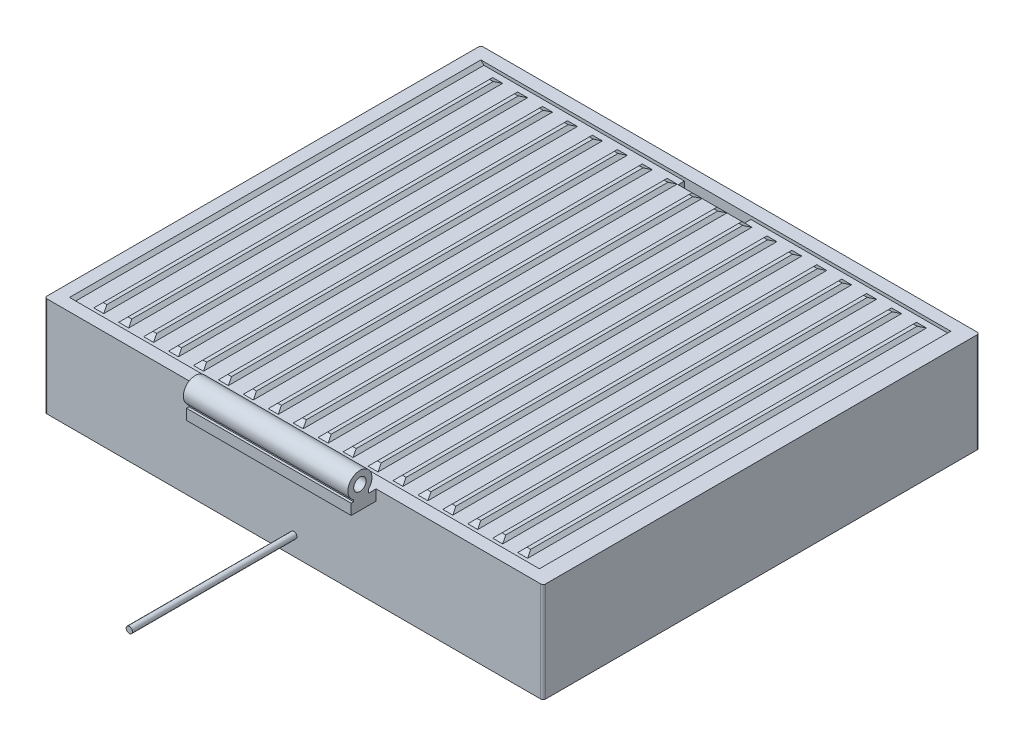
SolidWorks part; units mm, degrees
ref_plane "Front Plane" through (0, 0, 0) normal (0, 0, 1) x (1, 0, 0)
ref_plane "Top Plane" through (0, 0, 0) normal (0, 1, 0) x (1, 0, 0)
ref_plane "Right Plane" through (0, 0, 0) normal (1, 0, 0) x (0, 0, -1)
sketch "Sketch1" plane through (0, 0, 0) normal (0, 0, 1) x (1, 0, 0)
  line L1 (-200, 40) -> (200, 40)
  line L2 (-200, 40) -> (-200, -40)
  line L3 (-200, -40) -> (200, -40)
  line L4 (200, 40) -> (200, -40)
  line L5 (-200, 40) -> (200, -40) construction
  line L6 (-200, -40) -> (200, 40) construction
  point P0 (0, 0)
  dimension "D1" = 400
  dimension "D2" = 80
extrude "Boss-Extrude1" add sketch "Sketch1" along normal mid plane 350
sketch "Sketch2" plane through (0, 0, 0) normal (0, 0, 1) x (1, 0, 0)
  line L0 (200, 40) -> (-200, 40) construction
  line L1 (-190, 40) -> (-173, 40)
  line L14 (-190, 40) -> (-187.5, 37.5)
  line L15 (-187.5, 37.5) -> (-175.5, 37.5)
  line L16 (-175.5, 37.5) -> (-173, 40)
  line L17 (-173, 40) -> (-190, 40)
  line L18 (-170, 40) -> (-167.5, 37.5)
  line L19 (-167.5, 37.5) -> (-155.5, 37.5)
  line L20 (-155.5, 37.5) -> (-153, 40)
  line L21 (-170, 40) -> (-153, 40)
  line L22 (-150, 40) -> (-147.5, 37.5)
  line L23 (-147.5, 37.5) -> (-135.5, 37.5)
  line L24 (-135.5, 37.5) -> (-133, 40)
  line L25 (-150, 40) -> (-133, 40)
  line L26 (-130, 40) -> (-127.5, 37.5)
  line L27 (-127.5, 37.5) -> (-115.5, 37.5)
  line L28 (-115.5, 37.5) -> (-113, 40)
  line L29 (-130, 40) -> (-113, 40)
  line L30 (-110, 40) -> (-107.5, 37.5)
  line L31 (-107.5, 37.5) -> (-95.5, 37.5)
  line L32 (-95.5, 37.5) -> (-93, 40)
  line L33 (-110, 40) -> (-93, 40)
  line L34 (-90, 40) -> (-87.5, 37.5)
  line L35 (-87.5, 37.5) -> (-75.5, 37.5)
  line L36 (-75.5, 37.5) -> (-73, 40)
  line L37 (-90, 40) -> (-73, 40)
  line L38 (-70, 40) -> (-67.5, 37.5)
  line L39 (-67.5, 37.5) -> (-55.5, 37.5)
  line L40 (-55.5, 37.5) -> (-53, 40)
  line L41 (-70, 40) -> (-53, 40)
  line L42 (-50, 40) -> (-47.5, 37.5)
  line L43 (-47.5, 37.5) -> (-35.5, 37.5)
  line L44 (-35.5, 37.5) -> (-33, 40)
  line L45 (-50, 40) -> (-33, 40)
  line L46 (-30, 40) -> (-27.5, 37.5)
  line L47 (-27.5, 37.5) -> (-15.5, 37.5)
  line L48 (-15.5, 37.5) -> (-13, 40)
  line L49 (-30, 40) -> (-13, 40)
  line L50 (-10, 40) -> (-7.5, 37.5)
  line L51 (-7.5, 37.5) -> (4.5, 37.5)
  line L52 (4.5, 37.5) -> (7, 40)
  line L53 (-10, 40) -> (7, 40)
  line L54 (10, 40) -> (12.5, 37.5)
  line L55 (12.5, 37.5) -> (24.5, 37.5)
  line L56 (24.5, 37.5) -> (27, 40)
  line L57 (10, 40) -> (27, 40)
  line L58 (30, 40) -> (32.5, 37.5)
  line L59 (32.5, 37.5) -> (44.5, 37.5)
  line L60 (44.5, 37.5) -> (47, 40)
  line L61 (30, 40) -> (47, 40)
  line L62 (50, 40) -> (52.5, 37.5)
  line L63 (52.5, 37.5) -> (64.5, 37.5)
  line L64 (64.5, 37.5) -> (67, 40)
  line L65 (50, 40) -> (67, 40)
  line L66 (70, 40) -> (72.5, 37.5)
  line L67 (72.5, 37.5) -> (84.5, 37.5)
  line L68 (84.5, 37.5) -> (87, 40)
  line L69 (70, 40) -> (87, 40)
  line L70 (90, 40) -> (92.5, 37.5)
  line L71 (92.5, 37.5) -> (104.5, 37.5)
  line L72 (104.5, 37.5) -> (107, 40)
  line L73 (90, 40) -> (107, 40)
  line L74 (110, 40) -> (112.5, 37.5)
  line L75 (112.5, 37.5) -> (124.5, 37.5)
  line L76 (124.5, 37.5) -> (127, 40)
  line L77 (110, 40) -> (127, 40)
  line L78 (130, 40) -> (132.5, 37.5)
  line L79 (132.5, 37.5) -> (144.5, 37.5)
  line L80 (144.5, 37.5) -> (147, 40)
  line L81 (130, 40) -> (147, 40)
  line L82 (150, 40) -> (152.5, 37.5)
  line L83 (152.5, 37.5) -> (164.5, 37.5)
  line L84 (164.5, 37.5) -> (167, 40)
  line L85 (150, 40) -> (167, 40)
  line L86 (170, 40) -> (172.5, 37.5)
  line L87 (172.5, 37.5) -> (184.5, 37.5)
  line L88 (184.5, 37.5) -> (187, 40)
  line L89 (170, 40) -> (187, 40)
  dimension "D1" = 12
  dimension "D2" = 10
  dimension "D3" = 135
  dimension "D4" = 2.5
  dimension "D6" = 3
  dimension "D5" = 19
sketch "Sketch4" plane through (0, 0, 0) normal (1, 0, 0) x (0, 0, -1)
  line L0 (167.6557, 40) -> (164.2937, 36.6381)
  line L1 (-175, 40) -> (175, 40) construction
  line L2 (164.2937, 36.6381) -> (157.6386, 36.6381)
  line L3 (157.6386, 36.6381) -> (154.2766, 40)
extrude "Cut-Extrude2" cut sketch "Sketch2" against normal mid plane 330 contours L15 L16 L1 L14 | L21 L18 L19 L20 | L33 L30 L31 L32 | L25 L24 L23 L22 | L29 L28 L27 L26 | L35 L36 L37 L34 | L39 L40 L41 L38 | L43 L44 L45 L42 | L47 L48 L49 L46 | L51 L52 L53 L50 | L55 L56 L57 L54 | L59 L60 L61 L58 | L63 L64 L65 L62 | L67 L68 L69 L66 | L71 L72 L73 L70 | L75 L76 L77 L74 | L79 L80 L81 L78 | L83 L84 L85 L82 | L87 L88 L89 L86
sketch "Sketch5" plane through (0, 0, 0) normal (1, 0, 0) x (0, 0, -1)
  line L1 (-175, 40) -> (175, 40) construction
  line L2 (-165, 37.5) -> (-160, 37.5)
  line L3 (-160, 37.5) -> (-155, 40)
  line L4 (-155, 40) -> (-165, 40)
  line L5 (0, 44) -> (0, -44) construction
  line L6 (155, 40) -> (165, 40)
  line L7 (160, 37.5) -> (155, 40)
  line L8 (165, 37.5) -> (160, 37.5)
  line L9 (165, 40) -> (165, 37.5)
  line L10 (-165, 40) -> (-165, 37.5)
  dimension "D1" = 2.5
  dimension "D3" = 10
  dimension "D4" = 5
extrude "Cut-Extrude3" cut sketch "Sketch5" against normal mid plane 374
sketch "Sketch6" plane through (0, 0, -175) normal (0, 0, -1) x (-1, 0, 0)
  text T0 "<b>DR. FREEZY</b>" font "Century Gothic" height in points 30
extrude "Boss-Extrude2" add sketch "Sketch6" along normal blind 2 separate body
sketch "Sketch7" plane through (0, 0, 0) normal (1, 0, 0) x (0, 0, -1)
  line L1 (-175, 31.5) -> (-195, 31.5)
  line L2 (-175, 31.5) -> (-175, 40)
  line L3 (-175, 40) -> (-181, 40)
  line L4 (-195, 31.5) -> (-195, 40)
  line L5 (-175, 31.5) -> (-195, 40) construction
  line L6 (-175, 40) -> (-195, 31.5) construction
  line L7 (-175, 40) -> (-175, -40) construction
  line L8 (-175, 40) -> (175, 40) construction
  line L9 (-193, 40) -> (-193, 41.3936)
  line L10 (-181, 40) -> (-181, 43)
  line L11 (-193, 40) -> (-195, 40)
  arc A0 (-181, 43) -> (-193, 41.3936) centre (-188, 49.6667) ccw
  circle A1 centre (-188, 49.6667) radius 5
  point P0 (-185, 35.75)
  dimension "D6" = 10
  dimension "D1" = 8.5
  dimension "D2" = 20
  dimension "D3" = 3
  dimension "D4" = 6
  dimension "D5" = 2
extrude "Boss-Extrude3" add sketch "Sketch7" along normal mid plane 132
sketch "Sketch8" plane through (0, 0, 175) normal (0, 0, 1) x (1, 0, 0)
  circle A0 centre (0, -25) radius 2.5
  dimension "D1" = 5
  dimension "D2" = 25
extrude "Boss-Extrude4" add sketch "Sketch8" along normal blind 132
sketch "Sketch9" plane through (0, 37.5, 0) normal (0, 1, 0) x (1, 0, 0)
  line L0 (-187.5, 165) -> (187, 165) construction
  line L1 (-26.6865, 159.939) -> (26.6865, 159.939)
  line L2 (-26.6865, 159.939) -> (-26.6865, 165)
  line L3 (-26.6865, 165) -> (26.6865, 165)
  line L4 (26.6865, 159.939) -> (26.6865, 165)
  line L5 (-26.6865, 159.939) -> (26.6865, 165) construction
  line L6 (-26.6865, 165) -> (26.6865, 159.939) construction
  point P0 (0, 162.4695)
extrude "Cut-Extrude4" cut sketch "Sketch9" against normal blind 50
sketch "Sketch10" plane through (0, 0, -175) normal (0, 0, -1) x (-1, 0, 0)
  line L1 (-100, -25) -> (100, -25)
  line L2 (-100, -25) -> (-100, 25)
  line L3 (-100, 25) -> (100, 25)
  line L4 (100, -25) -> (100, 25)
  line L5 (-100, -25) -> (100, 25) construction
  line L6 (-100, 25) -> (100, -25) construction
  line L7 (-98, -23) -> (98, -23)
  line L8 (-98, -23) -> (-98, 23)
  line L9 (-98, 23) -> (98, 23)
  line L10 (98, -23) -> (98, 23)
  line L11 (-98, -23) -> (98, 23) construction
  line L12 (-98, 23) -> (98, -23) construction
  point P0 (0, 0)
  point P6 (0, 0)
  dimension "D1" = 2
  dimension "D2" = 2
  dimension "D3" = 50
  dimension "D4" = 200
extrude "Cut-Extrude5" cut sketch "Sketch10" against normal blind 330
sketch "Sketch11" plane through (0, 0, 0) normal (1, 0, 0) x (0, 0, -1)
  line L0 (175, 10) -> (190, 10)
  line L1 (175, -40) -> (175, 40) construction
  line L2 (190, 10) -> (190, 0)
  line L3 (190, 0) -> (185, 0)
  line L4 (185, 0) -> (185, 5)
  line L5 (185, 5) -> (175, 5)
  line L6 (175, 5) -> (175, 10)
  dimension "D1" = 5
  dimension "D2" = 5
  dimension "D3" = 10
  dimension "D4" = 10
extrude "Boss-Extrude5" add sketch "Sketch11" along normal mid plane 50
sketch "Sketch12" plane through (0, 0, -175) normal (0, 0, -1) x (-1, 0, 0)
  line L0 (-200, 40) -> (200, 40) construction
  line L1 (-200, -40) -> (-200, 40) construction
  circle A0 centre (-182.5, 27.5) radius 6.0232
  circle A1 centre (-162.5, 27.5) radius 6.0232
  point P4 (0, 0)
  dimension "D1" = 12.5
  dimension "D2" = 17.5
  dimension "D3" = 20
extrude "Boss-Extrude6" add sketch "Sketch12" along normal blind 3 separate body
sketch "Sketch13" plane through (0, 0, -175) normal (0, 0, -1) x (-1, 0, 0)
  line L0 (-200, -40) -> (-200, 40) construction
  line L1 (-188.5, 12.5) -> (-138.5, 12.5)
  line L2 (-188.5, 12.5) -> (-188.5, 7.5)
  line L3 (-188.5, 7.5) -> (-138.5, 7.5)
  line L4 (-138.5, 12.5) -> (-138.5, 7.5)
  line L5 (-188.5, 12.5) -> (-138.5, 7.5) construction
  line L6 (-188.5, 7.5) -> (-138.5, 12.5) construction
  line L7 (-200, 40) -> (200, 40) construction
  point P0 (-163.5, 10)
  dimension "D1" = 5
  dimension "D2" = 50
  dimension "D3" = 11.5
  dimension "D4" = 30
extrude "Cut-Extrude6" cut sketch "Sketch13" against normal blind 3
sketch "Sketch14" plane through (0, 0, -172) normal (0, 0, -1) x (-1, 0, 0)
  line L1 (-177.5, 12) -> (-187.5, 12)
  line L2 (-177.5, 12) -> (-177.5, 8)
  line L3 (-177.5, 8) -> (-187.5, 8)
  line L4 (-187.5, 12) -> (-187.5, 8)
  line L5 (-177.5, 12) -> (-187.5, 8) construction
  line L6 (-177.5, 8) -> (-187.5, 12) construction
  line L8 (-188.5, 12.5) -> (-188.5, 7.5) construction
  line L9 (-138.5, 12.5) -> (-188.5, 12.5) construction
  point P0 (-182.5, 10)
  dimension "D1" = 4
  dimension "D2" = 10
  dimension "D3" = 1
  dimension "D4" = 0.5
extrude "Boss-Extrude7" add sketch "Sketch14" along normal blind 6 separate body
sketch "Sketch15" plane through (0, 0, -175) normal (0, 0, -1) x (-1, 0, 0)
  line L0 (-188.5, 12.5) -> (-188.5, 7.5) construction
  line L1 (-188.5, 3.5) -> (-184.5, 3.5)
  line L2 (-188.5, 3.5) -> (-188.5, 4.5)
  line L3 (-188.5, 4.5) -> (-184.5, 4.5)
  line L4 (-184.5, 3.5) -> (-184.5, 4.5)
  line L5 (-188.5, 3.5) -> (-184.5, 4.5) construction
  line L6 (-188.5, 4.5) -> (-184.5, 3.5) construction
  line L7 (-188.5, 7.5) -> (-138.5, 7.5) construction
  line L8 (-138.5, 4.5) -> (-138.5, 3.5)
  line L9 (-138.5, 3.5) -> (-139.5, 3.5)
  line L10 (-139.5, 3.5) -> (-139.5, 2.5)
  line L11 (-139.5, 2.5) -> (-140.5, 2.5)
  line L12 (-140.5, 2.5) -> (-140.5, 3.5)
  line L13 (-140.5, 3.5) -> (-141.5, 3.5)
  line L14 (-141.5, 3.5) -> (-141.5, 4.5)
  line L15 (-141.5, 4.5) -> (-140.5, 4.5)
  line L16 (-140.5, 4.5) -> (-140.5, 5.5)
  line L17 (-140.5, 5.5) -> (-139.5, 5.5)
  line L18 (-139.5, 5.5) -> (-139.5, 4.5)
  line L19 (-139.5, 4.5) -> (-138.5, 4.5)
  line L20 (-138.5, 7.5) -> (-138.5, 12.5) construction
  point P0 (-186.5, 4)
  point P23 (-141.5, 4)
  dimension "D1" = 4
  dimension "D2" = 1
  dimension "D3" = 3
  dimension "D4" = 1
  dimension "D5" = 1
  dimension "D6" = 1
  dimension "D7" = 1
extrude "Boss-Extrude8" add sketch "Sketch15" along normal blind 1 separate body
fillet "Fillet2" radius 2 4 edges at (-200, 0, -175) (-200, 0, 175) (200, 0, 175) (200, 0, -175)
